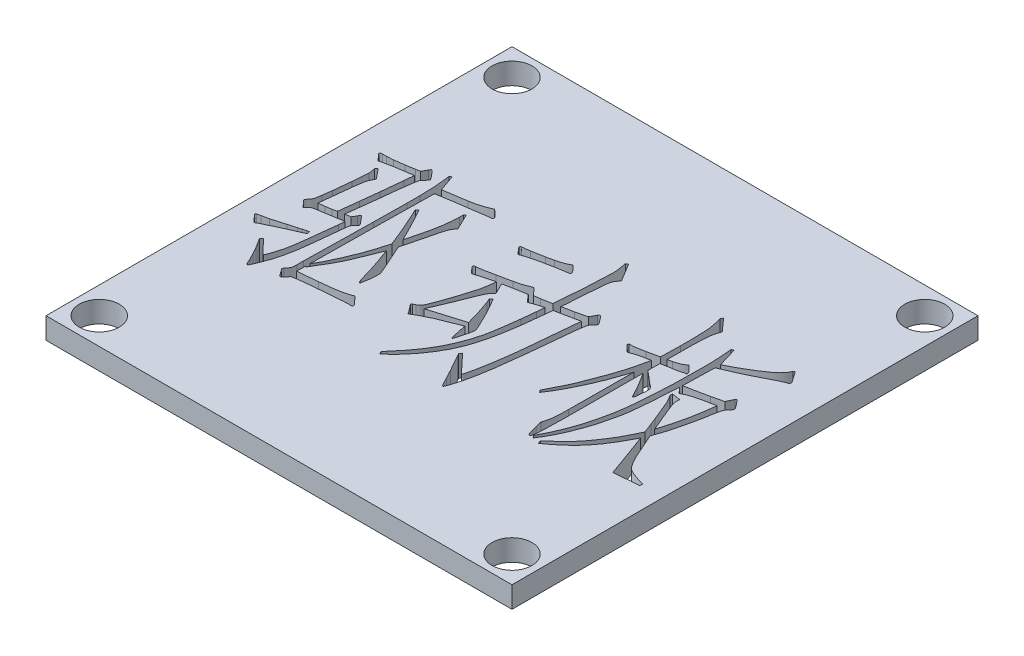
SolidWorks part; units mm, degrees
ref_plane "前视基准面" through (0, 0, 0) normal (0, 0, 1) x (1, 0, 0)
ref_plane "上视基准面" through (0, 0, 0) normal (0, 1, 0) x (1, 0, 0)
ref_plane "右视基准面" through (0, 0, 0) normal (1, 0, 0) x (0, 0, -1)
sketch "草图1" plane through (0, 0, 0) normal (0, 1, 0) x (1, 0, 0)
  line L1 (-17.5, -17.5) -> (17.5, -17.5)
  line L2 (-17.5, -17.5) -> (-17.5, 17.5)
  line L3 (-17.5, 17.5) -> (17.5, 17.5)
  line L4 (17.5, -17.5) -> (17.5, 17.5)
  line L5 (-17.5, -17.5) -> (17.5, 17.5) construction
  line L6 (-17.5, 17.5) -> (17.5, -17.5) construction
  point P0 (0, 0)
  dimension "D1" = 35
  dimension "D2" = 35
extrude "凸台-拉伸1" add sketch "草图1" along normal blind 1.6
sketch "草图2" plane through (0, 1.6, 0) normal (0, 1, 0) x (1, 0, 0)
  circle A0 centre (-15.5, 15.5) radius 1.5
  circle A1 centre (15.5, 15.5) radius 1.5
  circle A2 centre (15.5, -15.5) radius 1.5
  circle A3 centre (-15.5, -15.5) radius 1.5
  dimension "D1" = 15.5
  dimension "D2" = 15.5
  dimension "D3" = 15.5
  dimension "D4" = 15.5
  dimension "D5" = 15.5
  dimension "D6" = 15.5
  dimension "D8" = 15.5
  dimension "D9" = 3
  dimension "D10" = 3
  dimension "D11" = 3
  dimension "D12" = 3
  dimension "D7" = 15.5
extrude "切除-拉伸1" cut sketch "草图2" against normal through all
sketch "草图3" plane through (0, 1.6, 0) normal (0, 1, 0) x (1, 0, 0)
  text T0 "驱动板" font "汉仪长仿宋体" height in points 42
extrude "切除-拉伸2" cut sketch "草图3" against normal blind 1.6
